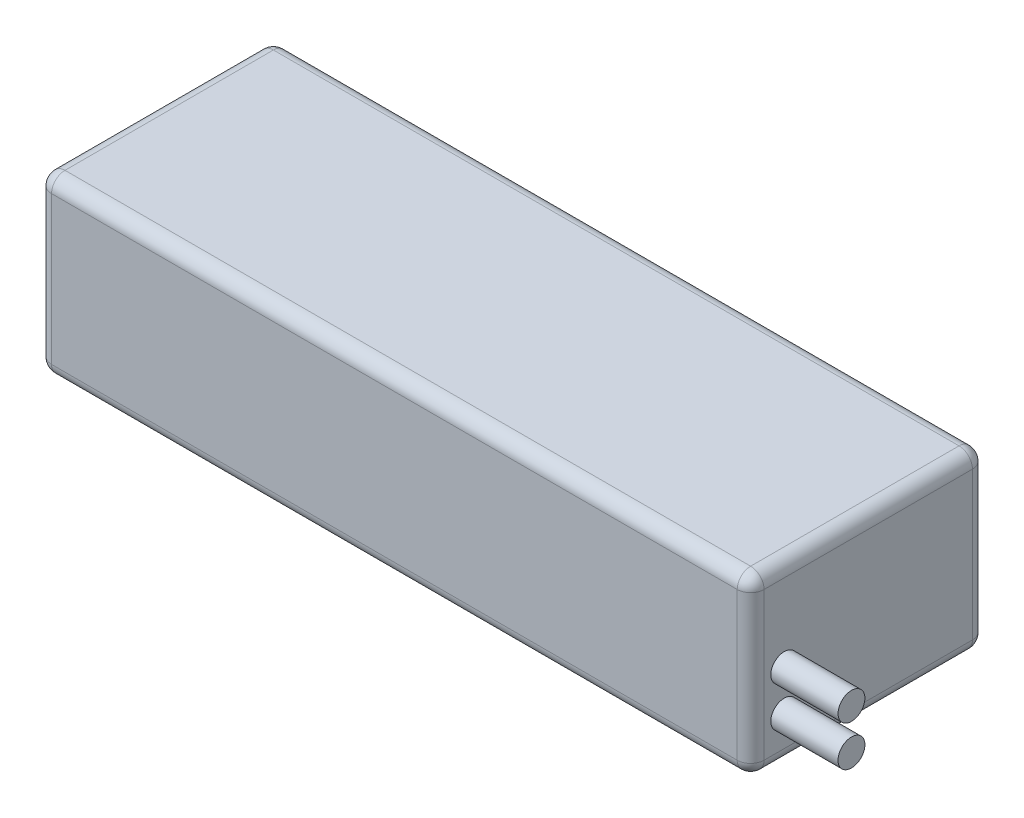
SolidWorks part; units mm, degrees
ref_plane "Front Plane" through (0, 0, 0) normal (0, 0, 1) x (1, 0, 0)
ref_plane "Top Plane" through (0, 0, 0) normal (0, 1, 0) x (1, 0, 0)
ref_plane "Right Plane" through (0, 0, 0) normal (1, 0, 0) x (0, 0, -1)
sketch "Sketch1" plane through (0, 0, 0) normal (0, 1, 0) x (1, 0, 0)
  line L1 (-53, 17.5) -> (53, 17.5)
  line L2 (-53, 17.5) -> (-53, -17.5)
  line L3 (-53, -17.5) -> (53, -17.5)
  line L4 (53, 17.5) -> (53, -17.5)
  line L5 (-53, 17.5) -> (53, -17.5) construction
  line L6 (-53, -17.5) -> (53, 17.5) construction
  point P0 (0, 0)
  dimension "D1" = 106
  dimension "D2" = 35
extrude "Boss-Extrude1" add sketch "Sketch1" along normal blind 26
fillet "Fillet1" radius 2 12 edges at (0, 0, 17.5) (0, 0, -17.5) (0, 26, -17.5) (0, 26, 17.5) (-53, 13, 17.5) (53, 13, 17.5) (-53, 0, 0) (-53, 26, 0) (-53, 13, -17.5) (53, 13, -17.5) (53, 0, 0) (53, 26, 0)
sketch "Sketch2" plane through (53, 0, 0) normal (1, 0, 0) x (0, 0, -1)
  line L2 (-12.5, 24) -> (-12.5, 2) construction
  line L3 (15.5, 24) -> (-15.5, 24) construction
  line L4 (-15.5, 2) -> (15.5, 2) construction
  line L5 (-15.5, 24) -> (-15.5, 2) construction
  circle A0 centre (-12.5, 6.5) radius 2
  circle A1 centre (-12.5, 12.5) radius 2
  dimension "D1" = 4
  dimension "D2" = 4
  dimension "D3" = 3
  dimension "D4" = 6
  dimension "D5" = 4.5
extrude "Boss-Extrude2" add sketch "Sketch2" along normal blind 10
